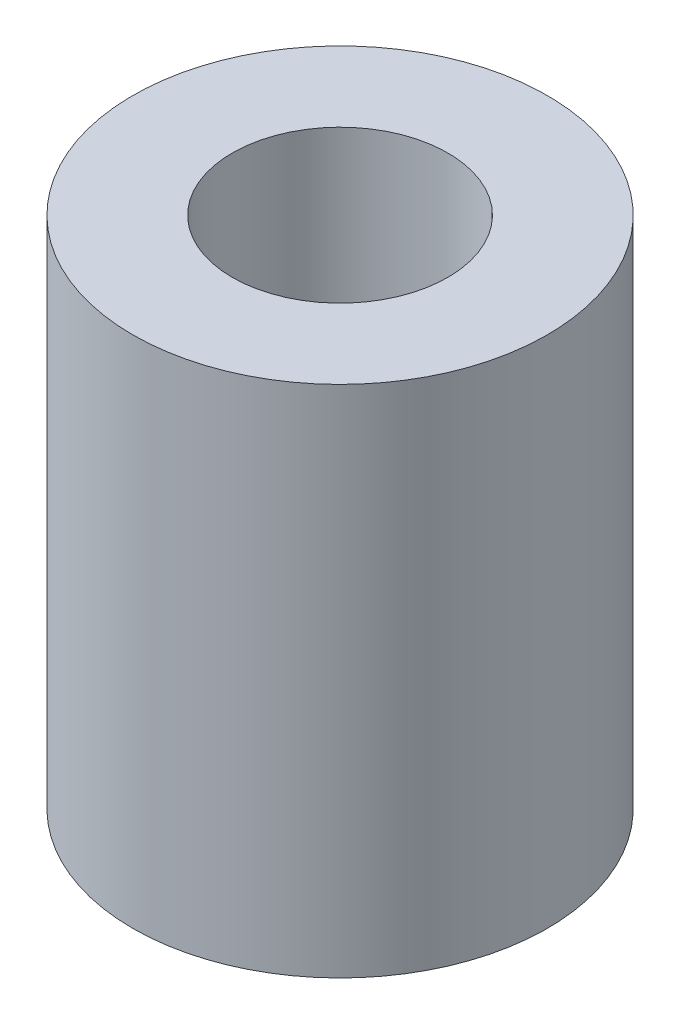
SolidWorks part; units mm, degrees
ref_plane "Face" through (0, 0, 0) normal (0, 0, 1) x (1, 0, 0)
ref_plane "Dessus" through (0, 0, 0) normal (0, 1, 0) x (1, 0, 0)
ref_plane "Droite" through (0, 0, 0) normal (1, 0, 0) x (0, 0, -1)
sketch "Esquisse1" plane through (0, 0, 0) normal (0, 1, 0) x (1, 0, 0)
  circle A0 centre (0, 0) radius 12.5
  circle A1 centre (0, 0) radius 6.5
  dimension "D1" = 25
  dimension "D2" = 13
extrude "Extrusion1" add sketch "Esquisse1" along normal blind 31
